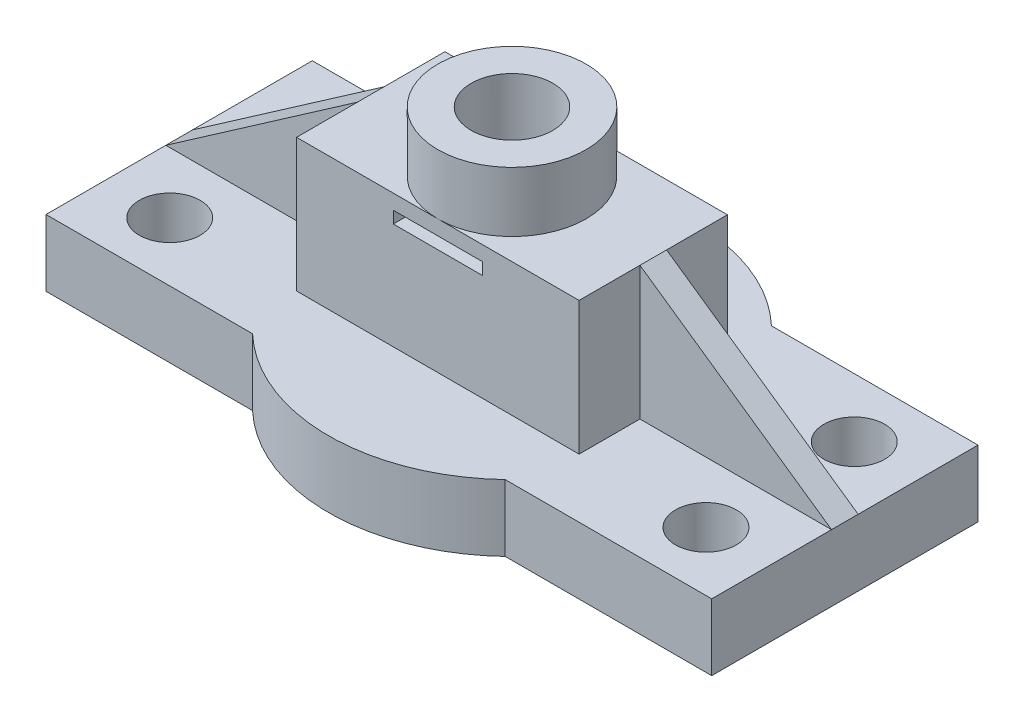
SolidWorks part; units mm, degrees
ref_plane "Front Plane" through (0, 0, 0) normal (0, 0, 1) x (1, 0, 0)
ref_plane "Top Plane" through (0, 0, 0) normal (0, 1, 0) x (1, 0, 0)
ref_plane "Right Plane" through (0, 0, 0) normal (1, 0, 0) x (0, 0, -1)
sketch "Sketch2" plane through (0, 0, 0) normal (0, 1, 0) x (1, 0, 0)
  line L0 (-64.2123, 0) -> (74.1438, 0) construction
  line L1 (-50, 20) -> (-18.9742, 20)
  line L2 (0, 50.3425) -> (0, -43.6644) construction
  line L3 (50, 20) -> (50, -20)
  line L4 (-50, 20) -> (-50, -20)
  line L5 (-50, -20) -> (-18.9742, -20)
  line L6 (18.9742, 20) -> (50, 20)
  line L7 (18.9742, -20) -> (50, -20)
  arc A0 (-18.9742, -20) -> (18.9742, -20) centre (0, 0) ccw
  arc A1 (18.9742, 20) -> (-18.9742, 20) centre (0, 0) ccw
  circle A2 centre (-40.2746, 11.1391) radius 4.5669
  circle A3 centre (-40.2746, -11.1391) radius 4.5669
  circle A4 centre (40.2746, -11.1391) radius 4.5669
  circle A5 centre (40.2746, 11.1391) radius 4.5669
  point P8 (0, -20)
  point P10 (0, 20)
  point P12 (-50, 0)
  point P13 (50, 0)
  point P20 (-40.2746, 11.1391)
  dimension "D1" = 50
  dimension "D2" = 20
extrude "Boss-Extrude1" add sketch "Sketch2" along normal blind 10
sketch "Sketch3" plane through (0, 10, 0) normal (0, 1, 0) x (1, 0, 0)
  line L0 (-40.4944, 0) -> (38.4429, 0) construction
  line L1 (-21.2181, 11.1391) -> (21.2181, 11.1391)
  line L2 (0, 23.853) -> (0, -21.0334) construction
  line L7 (-21.2181, -11.1391) -> (21.2181, -11.1391)
  line L8 (21.2181, 11.1391) -> (21.2181, -11.1391)
  line L9 (-21.2181, 11.1391) -> (-21.2181, -11.1391)
  point P11 (0, 11.1391)
extrude "Boss-Extrude2" add sketch "Sketch3" along normal blind 20
ref_plane "Plane2" through (0, 0, 0) normal (0, 0, 1) x (1, 0, 0)
sketch "Sketch5" plane through (0, 0, 0) normal (0, 0, 1) x (1, 0, 0)
  line L0 (-21.2181, 30) -> (-50, 10)
rib "Rib2" sketch "Sketch5" sketch "Sketch5" thickness 4 extrusion direction parallel to sketch draft on no parameters "D1"=4
sketch "Sketch6" plane through (0, 0, 0) normal (0, 0, 1) x (1, 0, 0)
  line L0 (21.2181, 30) -> (50, 10)
  line L1 (50, 10) -> (21.2181, 10)
  line L2 (21.2181, 10) -> (21.2181, 30)
extrude "Boss-Extrude3" add sketch "Sketch6" along normal mid plane 4
sketch "Sketch7" plane through (0, 30, 0) normal (0, 1, 0) x (1, 0, 0)
  circle A0 centre (0, 0) radius 11.1391
extrude "Extrude-Thin1" add sketch "Sketch7" along normal blind 9 thin thin type one direction reverse wall 5
sketch "Sketch9" plane through (0, 30, 0) normal (0, 1, 0) x (1, 0, 0)
  circle A1 centre (0, 0) radius 6.1391
  circle A2 centre (0, 0) radius 6.1391
  dimension "D1" = 0
extrude "Cut-Extrude2" cut sketch "Sketch9" against normal through all
sketch "Sketch12" plane through (0, 0, 0) normal (0, -1, 0) x (1, 0, 0)
  circle A0 centre (0, 0) radius 10
extrude "Cut-Extrude4" cut sketch "Sketch12" against normal blind 19 draft 11.5
sketch "Sketch13" plane through (0, 0, 11.1391) normal (0, 0, 1) x (1, 0, 0)
  line L0 (0, 43.0994) -> (0, -1.1686) construction
  line L1 (-6.6902, 27.7815) -> (6.6902, 27.7815)
  line L2 (6.6902, 27.7815) -> (6.6902, 25.9816)
  line L3 (6.6902, 25.9816) -> (-6.6902, 25.9816)
  line L4 (-6.6902, 27.7815) -> (-6.6902, 25.9816)
  point P8 (0, 25.9816)
  point P9 (0, 27.7815)
extrude "Cut-Extrude5" cut sketch "Sketch13" against normal blind 9
